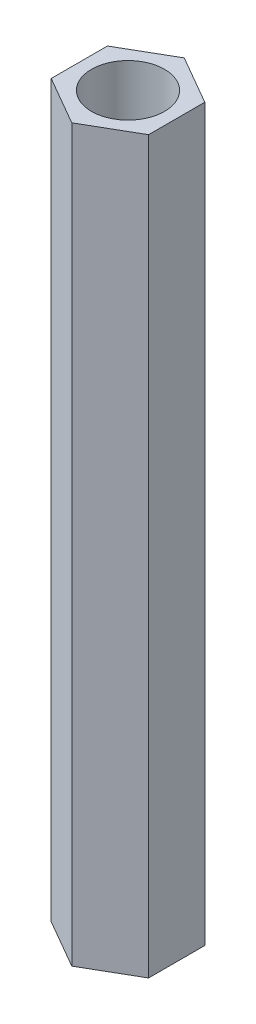
SolidWorks part; units mm, degrees
ref_plane "前视基准面" through (0, 0, 0) normal (0, 0, 1) x (1, 0, 0)
ref_plane "上视基准面" through (0, 0, 0) normal (0, 1, 0) x (1, 0, 0)
ref_plane "右视基准面" through (0, 0, 0) normal (1, 0, 0) x (0, 0, -1)
sketch "草图1" plane through (0, 0, 0) normal (0, 1, 0) x (1, 0, 0)
  line L1 (0, 2.3094) -> (-2, 1.1547)
  line L2 (-2, 1.1547) -> (-2, -1.1547)
  line L3 (-2, -1.1547) -> (0, -2.3094)
  line L4 (0, -2.3094) -> (2, -1.1547)
  line L5 (2, -1.1547) -> (2, 1.1547)
  line L6 (2, 1.1547) -> (0, 2.3094)
  circle A0 centre (0, 0) radius 1.5
  circle A1 centre (0, 0) radius 2 construction
  dimension "D1" = 3
  dimension "D2" = 4
extrude "凸台-拉伸1" add sketch "草图1" along normal blind 30
